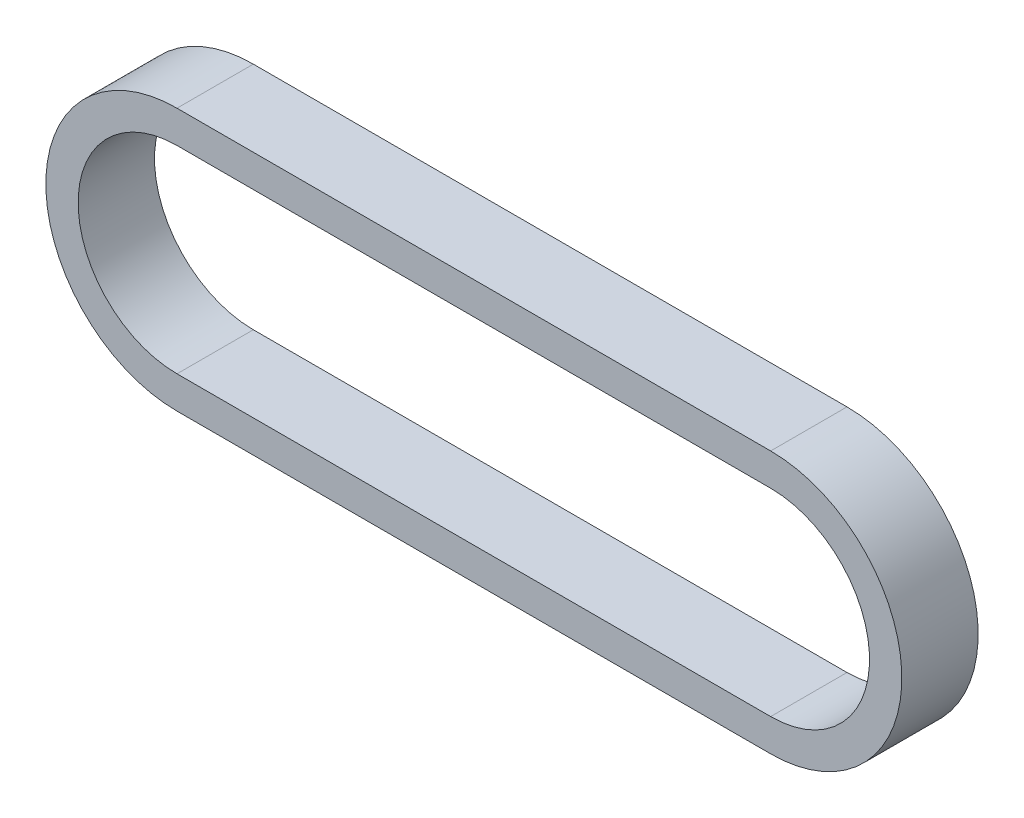
SolidWorks part; units mm, degrees
ref_plane "Front Plane" through (0, 0, 0) normal (0, 0, 1) x (1, 0, 0)
ref_plane "Top Plane" through (0, 0, 0) normal (0, 1, 0) x (1, 0, 0)
ref_plane "Right Plane" through (0, 0, 0) normal (1, 0, 0) x (0, 0, -1)
sketch "Sketch1" plane through (0, 0, 0) normal (0, 0, 1) x (1, 0, 0)
  line L0 (0, 14.324) -> (70, 14.324)
  line L1 (0, -14.324) -> (70, -14.324)
  line L2 (0, 0) -> (70, 0) construction
  arc A0 (0, 14.324) -> (0, -14.324) centre (0, 0) ccw
  arc A1 (70, -14.324) -> (70, 14.324) centre (70, 0) ccw
  dimension "D2" = 28.6479
  dimension "D3" = 28.6479
  dimension "D1" = 70
extrude "Extrude-Thin1" add sketch "Sketch1" along normal mid plane 9 thin thin type two direction wall 1.143 second wall 2.667
equation "\"Center Distance\"= 70mm"
equation "\"D1@Sketch1\"=\"Center Distance\""
equation "\"Pitch\"= 5mm"
equation "\"T1\"= 18"
equation "\"T2\"= 18"
equation "\"D2@Sketch1\" = \"Pitch\" * \"T1\" / 3.14159"
equation "\"D3@Sketch1\" = \"Pitch\" * \"T2\" / 3.14159"
equation "\"Teeth\"= 2 * \"Center Distance\" / \"Pitch\" + ( \"T1\" + \"T2\" ) / 2 + ( ( \"T2\" - \"T1\" ) / ( 2 * 3.14159 ) ) ^ 2 * \"Pitch\" / \"Center Distance\""
